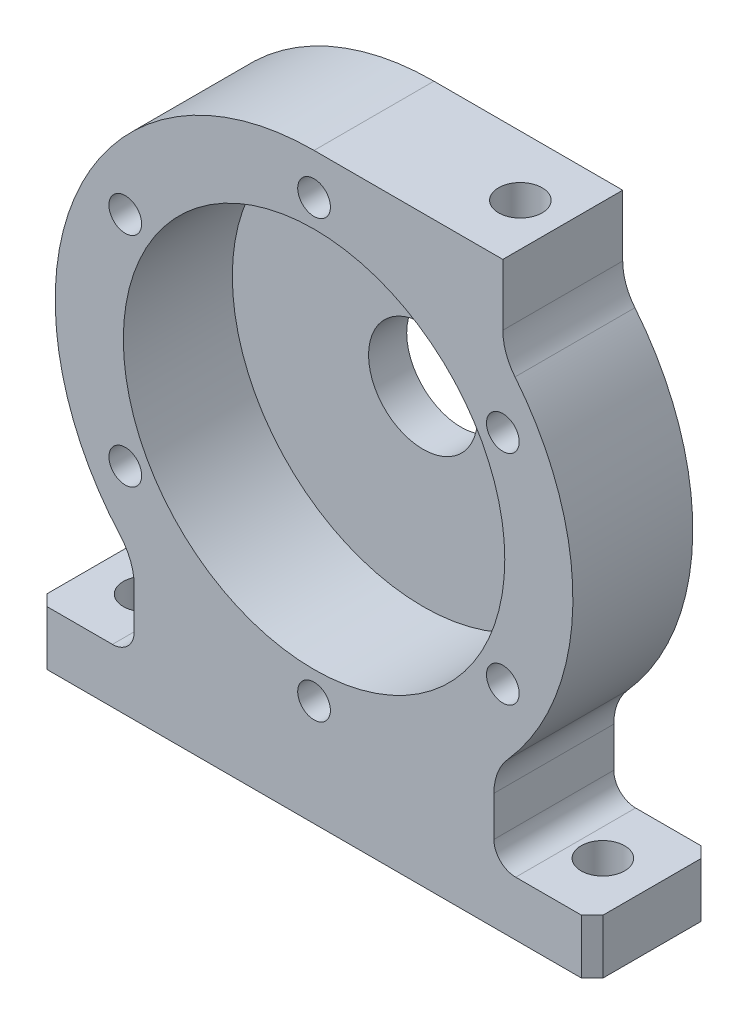
SolidWorks part; units mm, degrees
ref_plane "Front Plane" through (0, 0, 0) normal (0, 0, 1) x (1, 0, 0)
ref_plane "Top Plane" through (0, 0, 0) normal (0, 1, 0) x (1, 0, 0)
ref_plane "Right Plane" through (0, 0, 0) normal (1, 0, 0) x (0, 0, -1)
sketch "Sketch1" plane through (0, 0, 0) normal (0, 0, 1) x (1, 0, 0)
  line L0 (0, 128.2344) -> (0, -129.0551) construction
  line L1 (-171.6689, 0) -> (171.6689, 0) construction
  line L2 (-51.0418, 0) -> (51.0418, 0)
  line L3 (51.0418, 0) -> (51.0418, 10)
  line L4 (51.0418, 10) -> (37, 10)
  line L5 (33, 14) -> (33, 21.3261)
  line L6 (-33, 14) -> (-33, 21.3261)
  line L7 (-51.0418, 10) -> (-37, 10)
  line L8 (-51.0418, 0) -> (-51.0418, 10)
  line L9 (34.641, 95.7413) -> (34.641, 107)
  line L10 (34.641, 107) -> (0, 107)
  arc A0 (35.5217, 27.965) -> (36.8774, 89.4384) centre (0, 59.5) ccw
  arc A2 (33, 21.3261) -> (35.5217, 27.965) centre (43, 21.3261) cw
  arc A3 (37, 10) -> (33, 14) centre (37, 14) cw
  arc A4 (-37, 10) -> (-33, 14) centre (-37, 14) ccw
  arc A5 (-33, 21.3261) -> (-35.5217, 27.965) centre (-43, 21.3261) ccw
  arc A6 (0, 107) -> (-35.5217, 27.965) centre (0, 59.5) ccw
  arc A7 (34.641, 95.7413) -> (36.8774, 89.4384) centre (44.641, 95.7413) ccw
  point P24 (0, 0)
  point P28 (34.641, 92)
  dimension "D2" = 95
  dimension "D6" = 10
  dimension "D7" = 4
  dimension "D8" = 10
  dimension "D1" = 59.5
  dimension "D3" = 10
  dimension "D4" = 15
  dimension "D5" = 33
extrude "Boss-Extrude1" add sketch "Sketch1" along normal mid plane 22
sketch "Sketch2" plane through (0, 0, 11) normal (0, 0, 1) x (1, 0, 0)
  circle A0 centre (0, 59.5) radius 35
  dimension "D1" = 70
extrude "Cut-Extrude1" cut sketch "Sketch2" against normal blind 20
sketch "Sketch3" plane through (0, 0, -11) normal (0, 0, -1) x (-1, 0, 0)
  circle A0 centre (0, 59.5) radius 14
  dimension "D1" = 28
extrude "Boss-Extrude2" add sketch "Sketch3" along normal blind 5
sketch "Sketch4" plane through (0, 0, -16) normal (0, 0, -1) x (-1, 0, 0)
  circle A0 centre (0, 59.5) radius 10
  dimension "D1" = 20
extrude "Cut-Extrude2" cut sketch "Sketch4" against normal blind 55
fillet "Fillet1" radius 4 1 edges at (-14, 59.5, -11)
chamfer "Chamfer1" distance 2 angle 45 4 edges at (-51.0418, 5, -11) (51.0418, 5, -11) (51.0418, 5, 11) (-51.0418, 5, 11)
sketch "Sketch5" plane through (0, 10, 0) normal (0, 1, 0) x (1, 0, 0)
  circle A0 centre (-42, 0) radius 4
  circle A1 centre (42, 0) radius 4
  dimension "D1" = 8
  dimension "D2" = 8
  dimension "D3" = 84
  dimension "D4" = 42
extrude "Cut-Extrude3" cut sketch "Sketch5" against normal blind 10
sketch "Sketch6" plane through (0, 107, 0) normal (0, 1, 0) x (1, 0, 0)
  line L0 (-59.3547, 0) -> (80.6997, 0) construction
  line L1 (34.641, -11) -> (34.641, 11) construction
  circle A0 centre (26.861, 0) radius 4
  dimension "D1" = 8
  dimension "D2" = 7.78
extrude "Cut-Extrude4" cut sketch "Sketch6" against normal blind 31
sketch "Sketch7" plane through (0, 0, 11) normal (0, 0, 1) x (1, 0, 0)
  circle A0 centre (0, 59.5) radius 40 construction
  circle A1 centre (0, 99.5) radius 3
  circle A2 centre (34.641, 79.5) radius 3
  circle A3 centre (34.641, 39.5) radius 3
  circle A4 centre (0, 19.5) radius 3
  circle A5 centre (-34.641, 39.5) radius 3
  circle A6 centre (-34.641, 79.5) radius 3
  dimension "D1" = 80
  dimension "D2" = 6
  dimension "D3" = 6
extrude "Cut-Extrude5" cut sketch "Sketch7" against normal blind 6
